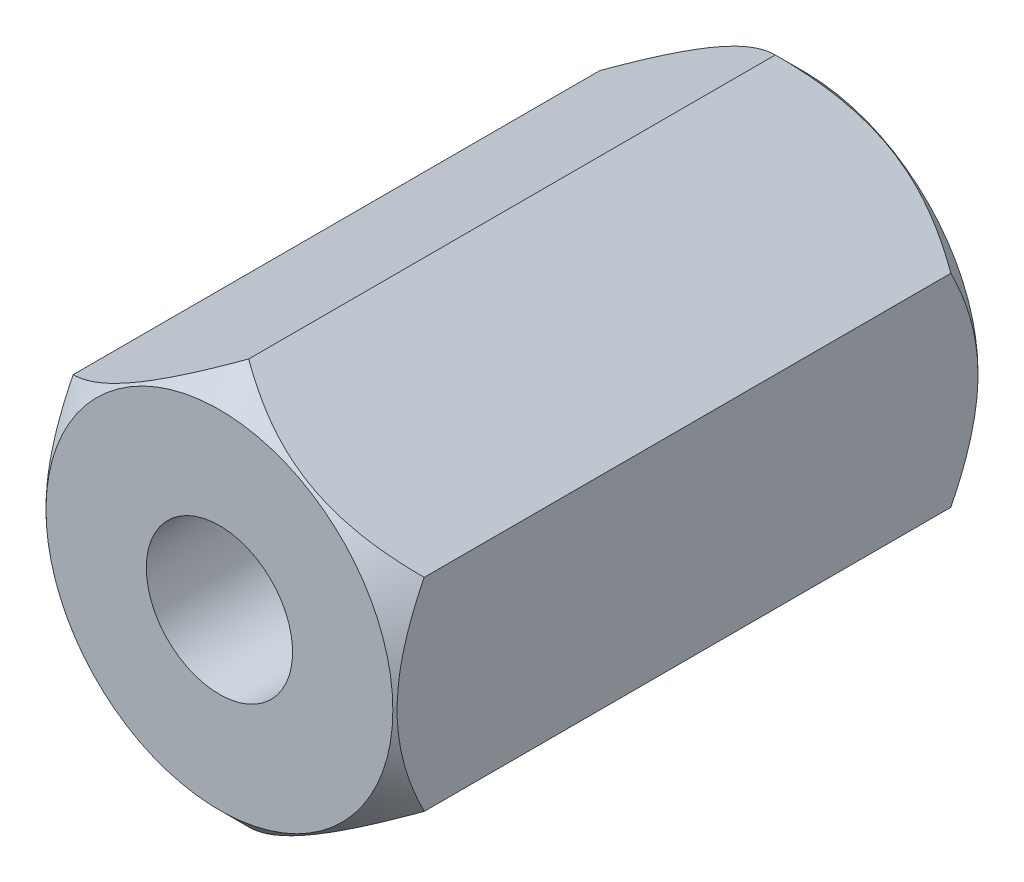
SolidWorks part; units mm, degrees
ref_plane "Plan de face" through (0, 0, 0) normal (0, 0, 1) x (1, 0, 0)
ref_plane "Plan de dessus" through (0, 0, 0) normal (0, 1, 0) x (1, 0, 0)
ref_plane "Plan de droite" through (0, 0, 0) normal (1, 0, 0) x (0, 0, -1)
sketch "Esquisse1" plane through (0, 0, 0) normal (0, 0, 1) x (1, 0, 0)
  line L1 (0, 3.4641) -> (-3, 1.7321)
  line L2 (-3, 1.7321) -> (-3, -1.7321)
  line L3 (-3, -1.7321) -> (0, -3.4641)
  line L4 (0, -3.4641) -> (3, -1.7321)
  line L5 (3, -1.7321) -> (3, 1.7321)
  line L6 (3, 1.7321) -> (0, 3.4641)
  circle A0 centre (0, 0) radius 3 construction
  dimension "D1" = 6
extrude "Boss.-Extru.1" add sketch "Esquisse1" along normal blind 10
sketch "Esquisse2" plane through (0, 0, 0) normal (1, 0, 0) x (0, 0, -1)
  line L0 (-10, 2.9641) -> (-9.5, 3.4641)
  line L1 (-14.5, 7.9641) -> (-9.5, 7.9641)
  line L2 (-14.5, 7.9641) -> (-14.5, 2.9641)
  line L3 (-14.5, 2.9641) -> (-10, 2.9641)
  line L4 (-9.5, 7.9641) -> (-9.5, 3.4641)
  line L5 (0, 2.9641) -> (4.5, 2.9641)
  line L6 (-0.5, 3.4641) -> (-0.5, 7.9641)
  line L7 (-0.5, 7.9641) -> (4.5, 7.9641)
  line L8 (4.5, 2.9641) -> (4.5, 7.9641)
  line L9 (-0.5, 3.4641) -> (0, 2.9641)
  line L10 (-10, 3.4641) -> (0, 3.4641) construction
  line L11 (-10, 1.7321) -> (-10, 3.4641) construction
  line L14 (0, 1.7321) -> (0, 3.4641) construction
  line L15 (-1000, 0) -> (49000, 0) construction
  point P1 (-9.5, 2.9641)
  point P4 (-0.5, 2.9641)
  dimension "D1" = 5
  dimension "D2" = 5
  dimension "D3" = 5
  dimension "D4" = 5
revolve "Enlèvement de matière-Révolution1" cut sketch "Esquisse2" angle 360 about L15
hole_wizard "Trou pour taraudage pour trou taraudé M31" positions "Esquisse4" profile "Esquisse3" hole size "M3" standard "Iso" end condition through all
sketch "Esquisse4" plane through (0, 0, 0) normal (0, 0, -1) x (-1, 0, 0)
  point P0 (0, 0)
sketch "Esquisse3" plane through (0, 0, 0) normal (1, 0, 0) x (0, 1, 0)
  line L0 (0, 0) -> (0, 10)
  line L1 (0, 10) -> (1.25, 10)
  line L2 (1.25, 10) -> (1.25, 0)
  line L5 (1.25, 0) -> (0, 0)
  line L11 (0, -6.35) -> (0, 107.95) construction
  dimension "Diamètre du perçage jusqu'au prochain" = 2.5
  dimension "Profondeur du perçage jusqu'au prochain" = 10
